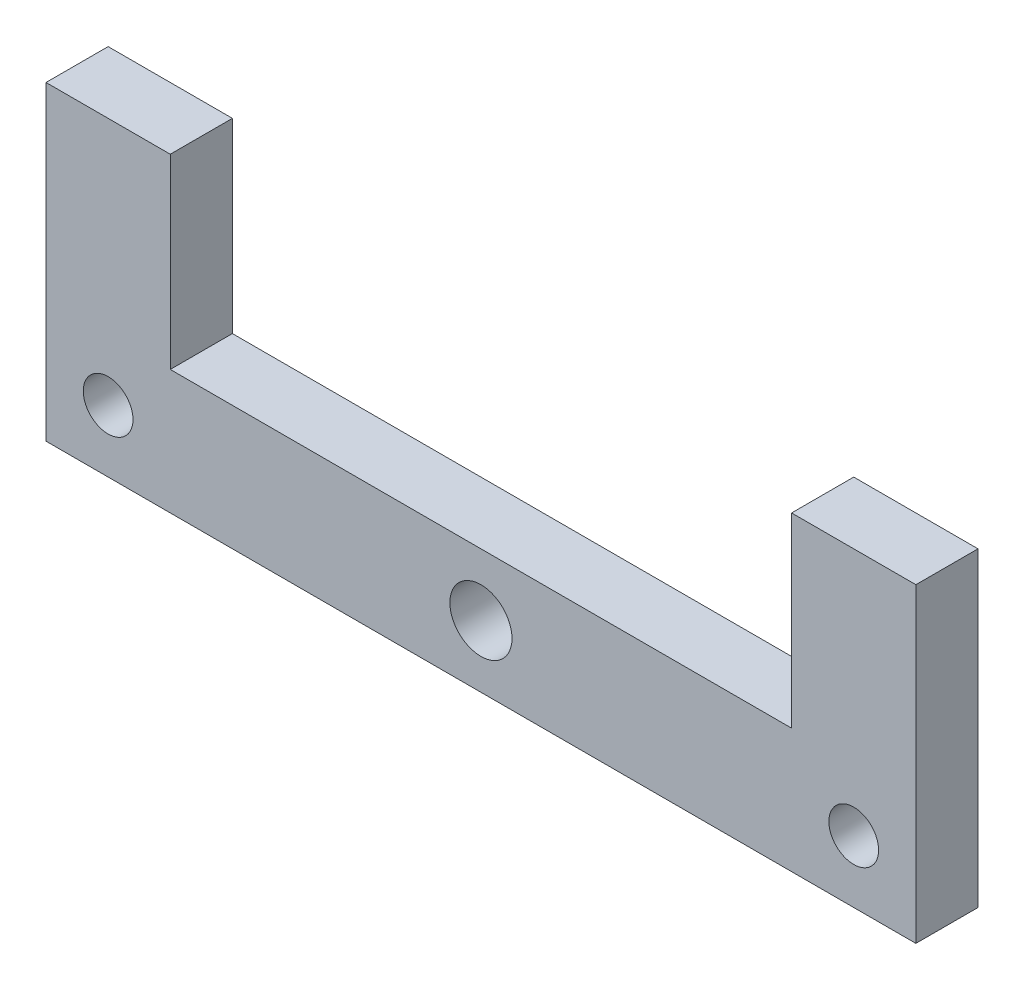
SolidWorks part; units mm, degrees
ref_plane "Plan de face" through (0, 0, 0) normal (0, 0, 1) x (1, 0, 0)
ref_plane "Plan de dessus" through (0, 0, 0) normal (0, 1, 0) x (1, 0, 0)
ref_plane "Plan de droite" through (0, 0, 0) normal (1, 0, 0) x (0, 0, -1)
sketch "Esquisse1" plane through (0, 0, 0) normal (0, 0, 1) x (1, 0, 0)
  line L0 (0, 0) -> (39.165, 0) construction
  line L1 (39.165, 0) -> (-46.8232, 0) construction
  line L2 (0, 0) -> (0, 19.9885) construction
  line L4 (-70, 10) -> (-70, -10)
  line L5 (-70, -10) -> (70, -10)
  line L6 (70, 10) -> (70, -10)
  line L8 (-50, 10) -> (50, 10)
  line L10 (-70, 10) -> (-70, 40)
  line L11 (-70, 40) -> (-50, 40)
  line L12 (-70, -10) -> (70, -10)
  line L13 (-50, 10) -> (-50, 40)
  line L15 (70, 10) -> (70, 40)
  line L16 (70, 40) -> (50, 40)
  line L17 (50, 10) -> (50, 40)
  circle A0 centre (0, 0) radius 5
  circle A1 centre (-60, 0) radius 4
  circle A2 centre (60, 0) radius 4
  dimension "D1" = 10
  dimension "D2" = 8
  dimension "D3" = 8
  dimension "D4" = 60
  dimension "D5" = 60
  dimension "D6" = 20
  dimension "D7" = 10
  dimension "D8" = 30
  dimension "D9" = 30
  dimension "D10" = 20
  dimension "D11" = 20
extrude "Boss.-Extru.1" add sketch "Esquisse1" along normal blind 10
